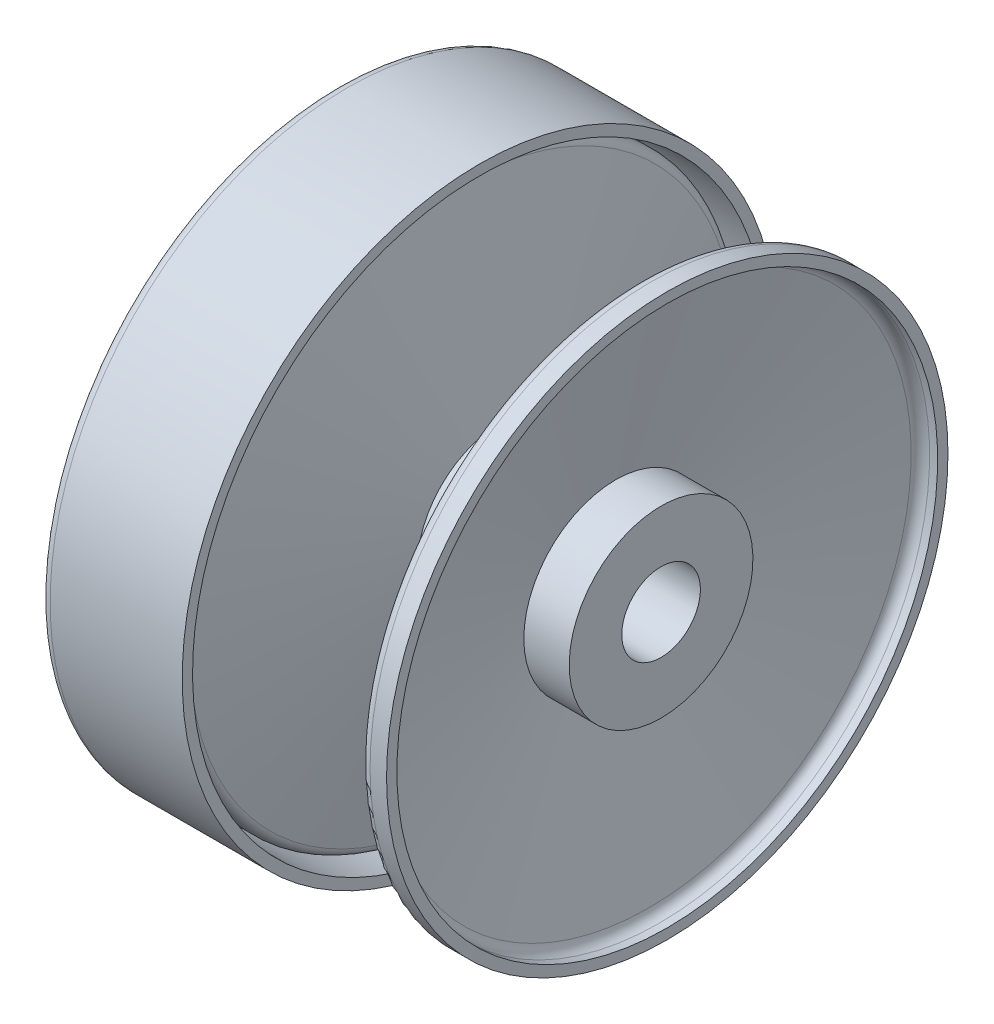
SolidWorks part; units mm, degrees
material "AISI 1020"
ref_plane "Спереди" through (0, 0, 0) normal (0, 0, 1) x (1, 0, 0)
ref_plane "Сверху" through (0, 0, 0) normal (0, 1, 0) x (1, 0, 0)
ref_plane "Справа" through (0, 0, 0) normal (1, 0, 0) x (0, 0, -1)
sketch "Эскиз1" plane through (0, 0, 0) normal (0, 0, 1) x (1, 0, 0)
  line L0 (-50, 0) -> (50, 0) construction
  line L1 (-36, 9.525) -> (48.5, 9.525)
  line L2 (48.5, 9.525) -> (48.5, 22.25)
  line L3 (48.5, 22.25) -> (37.5, 22.25)
  line L4 (37.5, 22.25) -> (46, 65.5)
  line L5 (46, 65.5) -> (50, 65.5)
  line L6 (50, 65.5) -> (50, 68)
  line L7 (50, 68) -> (43.9435, 68)
  line L8 (43.9435, 68) -> (34.51, 20)
  line L9 (-36, 4.25) -> (-41, 4.25)
  line L10 (-41, 4.25) -> (-41, 12.75)
  line L11 (-41, 12.75) -> (-50, 12.75)
  line L12 (-50, 12.75) -> (-50, 25.75)
  line L13 (-50, 25.75) -> (-41, 25.75)
  line L14 (-41, 25.75) -> (-41, 46.5)
  line L15 (-41, 46.5) -> (-30, 52)
  line L16 (-30, 52) -> (-30, 72)
  line L17 (-30, 72) -> (4.5, 72)
  line L18 (-36, 4.25) -> (-36, 9.525)
  line L19 (4.5, 72) -> (4.5, 69.5)
  line L20 (4.5, 69.5) -> (-15, 69.5)
  line L21 (34.51, 20) -> (9.4335, 20)
  line L22 (9.4335, 20) -> (0, 68)
  line L23 (0, 68) -> (-6.0565, 68)
  line L24 (-6.0565, 68) -> (-6.0565, 65.5)
  line L25 (-6.0565, 65.5) -> (-2.0565, 65.5)
  line L26 (-2.0565, 65.5) -> (6.4435, 22.25)
  line L27 (6.4435, 22.25) -> (-15, 22.25)
  line L28 (-15, 22.25) -> (-15, 69.5)
  point P2 (0, 0)
  point P16 (-30, 62)
  point P32 (-4.6659, 68)
  point P35 (0, 0)
  dimension "D1" = 100
  dimension "D2" = 19.05
  dimension "D3" = 44.5
  dimension "D4" = 11
  dimension "D5" = 1.5
  dimension "D6" = 2.5
  dimension "D7" = 136
  dimension "D8" = 40
  dimension "D9" = 2.5
  dimension "D10" = 4
  dimension "D11" = 8.5
  dimension "D12" = 5
  dimension "D13" = 9
  dimension "D14" = 51.5
  dimension "D15" = 93
  dimension "D16" = 104
  dimension "D17" = 144
  dimension "D18" = 9
  dimension "D19" = 11
  dimension "D20" = 25.5
  dimension "D21" = 34.5
  dimension "D22" = 2.5
  dimension "D23" = 50
  dimension "D24" = 15
revolve "Повернуть1" add sketch "Эскиз1" angle 360 about L0
fillet "Скругление1" radius 2.5 6 edges at (-41, -46.5, 0) (-30, -52, 0) (-30, -72, 0) (0, -68, 0) (43.9435, -68, 0) (46, -65.5, 0)
sketch "Эскиз2" plane through (-50, 0, 0) normal (-1, 0, 0) x (0, 0, 1)
  line L1 (0, 25.75) -> (-22.3002, 12.875)
  line L2 (-22.3002, 12.875) -> (-22.3002, -12.875)
  line L3 (-22.3002, -12.875) -> (0, -25.75)
  line L4 (0, -25.75) -> (22.3002, -12.875)
  line L5 (22.3002, -12.875) -> (22.3002, 12.875)
  line L6 (22.3002, 12.875) -> (0, 25.75)
  circle A0 centre (0, 0) radius 22.3002 construction
  circle A1 centre (0, 0) radius 25.75 construction
  point P11 (0, 0)
extrude "Вырез-Вытянуть1" cut sketch "Эскиз2" against normal up to surface (9 mm away) flip side to cut up to face at (-41, 44.9549, 0)
